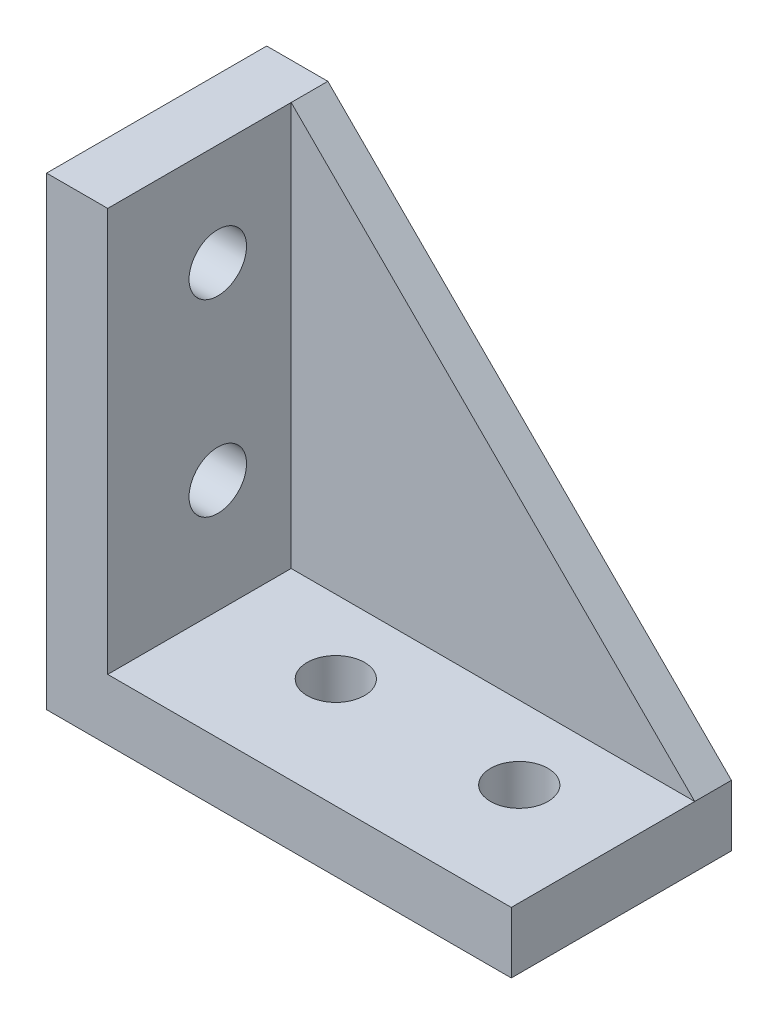
SolidWorks part; units mm, degrees
ref_plane "前视基准面" through (0, 0, 0) normal (0, 0, 1) x (1, 0, 0)
ref_plane "上视基准面" through (0, 0, 0) normal (0, 1, 0) x (1, 0, 0)
ref_plane "右视基准面" through (0, 0, 0) normal (1, 0, 0) x (0, 0, -1)
sketch "草图1" plane through (0, 0, 0) normal (0, 0, 1) x (1, 0, 0)
  line L0 (0, 38) -> (0, 0)
  line L1 (0, 0) -> (38, 0)
  line L2 (0, 38) -> (5, 38)
  line L3 (38, 0) -> (38, 5)
  line L4 (38, 5) -> (5, 5)
  line L5 (5, 5) -> (5, 38)
extrude "凸台-拉伸1" add sketch "草图1" along normal blind 18
other "角撑板1" parameters "D1"=3, "D2"=3, "D3"=0, "D4"=0, "D10"=5, "D11"=33, "D12"=33, "D13"=15, "D14"=45, "D15"=15
sketch "草图2" plane through (5, 5, 0) normal (0, 0, 1) x (1, 0, 0)
  line L0 (0, 0) -> (0, 33)
  line L1 (0, 0) -> (33, 0)
  line L2 (0, 33) -> (33, 0)
sketch "草图4" plane through (5, 0, 0) normal (1, 0, 0) x (0, 0, -1)
  circle A0 centre (-9, 29.65) radius 2.35
  circle A1 centre (-9, 14.25) radius 2.35
sketch "草图5" plane through (0, 5, 0) normal (0, 1, 0) x (1, 0, 0)
  circle A0 centre (29.65, -9) radius 2.35
  circle A1 centre (14.65, -9) radius 2.35
extrude "切除-拉伸1" cut sketch "草图4" against normal blind 13 and the other way blind 12
extrude "切除-拉伸2" cut sketch "草图5" against normal blind 12 and the other way blind 15
